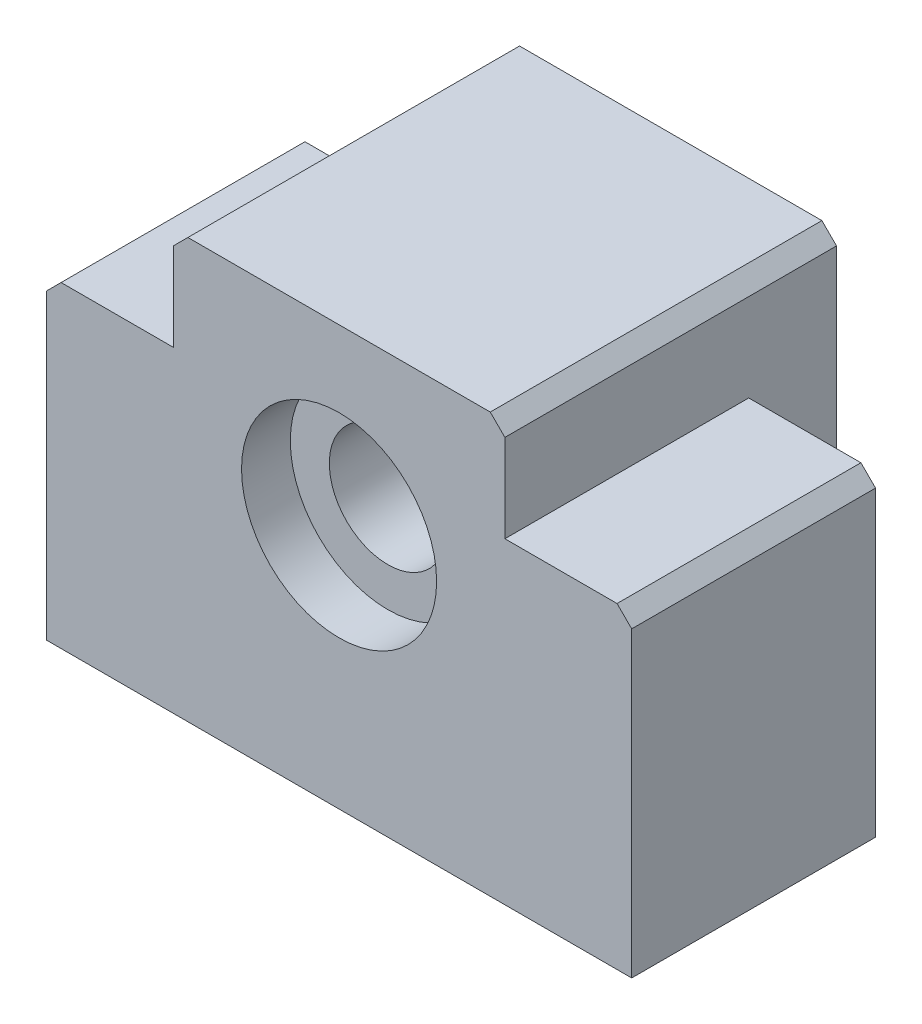
SolidWorks part; units mm, degrees
material "AISI 1045 Acero estirado en frío"
ref_plane "Alzado" through (0, 0, 0) normal (0, 0, 1) x (1, 0, 0)
ref_plane "Planta" through (0, 0, 0) normal (0, 1, 0) x (1, 0, 0)
ref_plane "Vista lateral" through (0, 0, 0) normal (1, 0, 0) x (0, 0, -1)
sketch "Croquis1" plane through (0, 0, 0) normal (0, 0, 1) x (1, 0, 0)
  line L0 (0, 16.25) -> (-13, 16.25) construction
  line L1 (-30, 16.25) -> (30, 16.25)
  line L2 (-30, 16.25) -> (-30, -16.25)
  line L3 (-30, -16.25) -> (30, -16.25)
  line L4 (30, 16.25) -> (30, -16.25)
  line L5 (-30, 16.25) -> (30, -16.25) construction
  line L6 (-30, -16.25) -> (30, 16.25) construction
  line L7 (0, 16.25) -> (13, 16.25) construction
  point P0 (0, 0)
  dimension "D1" = 60
  dimension "D2" = 32.5
extrude "Saliente-Extruir1" add sketch "Croquis1" along normal blind 25
ref_plane "Plano1" through (0, 0, 25) normal (0, 0, -1) x (-1, 0, 0)
sketch "Croquis2" plane through (0, 0, 25) normal (0, 0, -1) x (-1, 0, 0)
  line L0 (0, 0) -> (0, 16.25) construction
  line L1 (-30, 16.25) -> (30, 16.25) construction
  line L2 (0, 16.25) -> (17, 16.25) construction
  line L3 (0, 16.25) -> (-17, 16.25) construction
  line L4 (-17, 16.25) -> (-17, 26.75)
  line L5 (-17, 26.75) -> (17, 26.75)
  line L6 (17, 26.75) -> (17, 16.25)
  line L7 (-17, 16.25) -> (-17, -9.25)
  line L8 (-17, -9.25) -> (17, -9.25)
  line L9 (17, -9.25) -> (17, 16.25)
  line L10 (30, -16.25) -> (-30, -16.25) construction
  dimension "D1" = 10.5
  dimension "D2" = 7
  dimension "D3" = 17
  dimension "D4" = 17
extrude "Saliente-Extruir2" add sketch "Croquis2" along normal blind 34
sketch "Croquis3" plane through (0, 0, 25) normal (0, 0, -1) x (-1, 0, 0)
  line L0 (30, -16.25) -> (-30, -16.25) construction
  circle A0 centre (0, 8.95) radius 6
  dimension "D1" = 12
  dimension "D2" = 25.2
extrude "Cortar-Extruir1" cut sketch "Croquis3" along normal through all
chamfer "Chaflán1" distance 1.5 1 edges at (17, 26.75, 8)
chamfer "Chaflán2" distance 1.5 angle 45 1 edges at (-17, 26.75, 8)
chamfer "Chaflán3" distance 1.5 angle 45 2 edges at (-30, 16.25, 12.5) (30, 16.25, 12.5)
ref_plane "Plano2" through (0, 0, -9) normal (0, 0, 1) x (1, 0, 0)
sketch "Croquis5" plane through (0, 0, -9) normal (0, 0, 1) x (1, 0, 0)
  circle A0 centre (0, 8.95) radius 10
  dimension "D1" = 20
extrude "Cortar-Extruir2" cut sketch "Croquis5" along normal blind 15
ref_plane "Plano3" through (0, 0, 25) normal (0, 0, 1) x (1, 0, 0)
sketch "Croquis6" plane through (0, 0, 25) normal (0, 0, 1) x (1, 0, 0)
  circle A0 centre (0, 8.95) radius 10
  dimension "D1" = 20
extrude "Cortar-Extruir3" cut sketch "Croquis6" against normal blind 5
